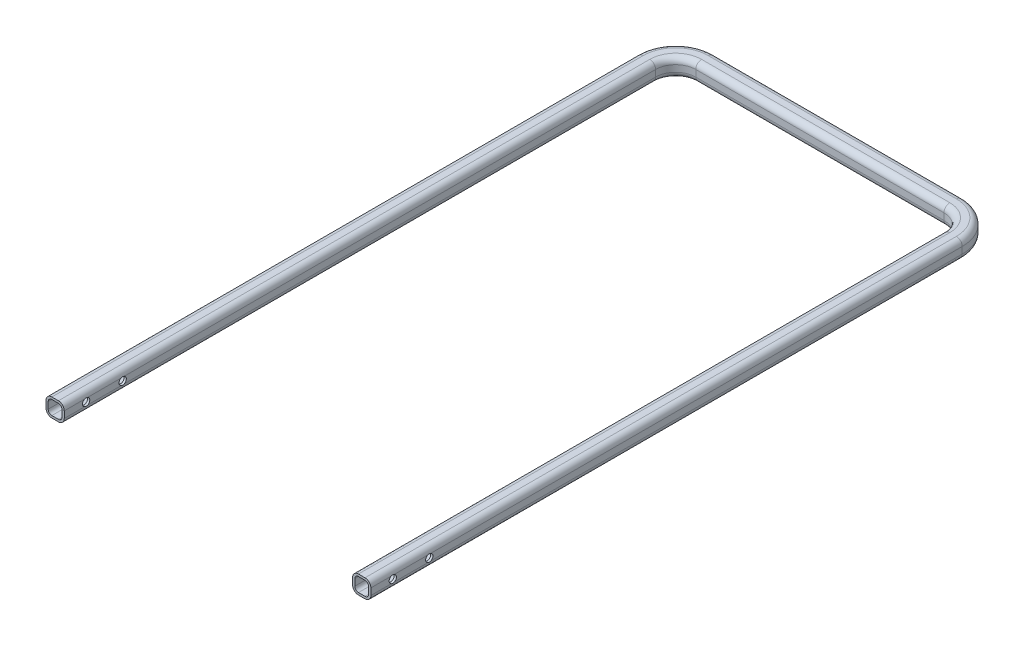
SolidWorks part; units mm, degrees
material "5052-H38, Rod (SS)"
ref_plane "Front Plane" through (0, 0, 0) normal (0, 0, 1) x (1, 0, 0)
ref_plane "Top Plane" through (0, 0, 0) normal (0, 1, 0) x (1, 0, 0)
ref_plane "Right Plane" through (0, 0, 0) normal (1, 0, 0) x (0, 0, -1)
sketch "Sketch1" plane through (0, 0, 0) normal (0, 1, 0) x (1, 0, 0)
  line L0 (0, 0) -> (0, 810)
  line L1 (40, 850) -> (380, 850)
  line L2 (420, 810) -> (420, 0)
  line L3 (0, 560) -> (420, 560) construction
  line L4 (0, 260) -> (420, 260) construction
  line L5 (420, 260) -> (420, 560) construction
  arc A0 (380, 850) -> (420, 810) centre (380, 810) cw
  arc A1 (40, 850) -> (0, 810) centre (40, 810) ccw
  point P7 (420, 850)
  point P10 (0, 850)
  dimension "D3" = 40
  dimension "D4" = 250
  dimension "D1" = 850
  dimension "D2" = 420
  dimension "D5" = 300
ref_plane "Plane1" through (0, 0, 0) normal (0, 0, 1) x (1, 0, 0)
sketch "Sketch3" plane through (0, 0, 0) normal (0, 0, 1) x (1, 0, 0)
  line L1 (-4.5, -9.5) -> (4.5, -9.5)
  line L2 (-9.5, -4.5) -> (-9.5, 4.5)
  line L3 (-4.5, 9.5) -> (4.5, 9.5)
  line L4 (9.5, -4.5) -> (9.5, 4.5)
  line L5 (-9.5, -9.5) -> (9.5, 9.5) construction
  line L6 (-9.5, 9.5) -> (9.5, -9.5) construction
  arc A0 (-4.5, 9.5) -> (-9.5, 4.5) centre (-4.5, 4.5) ccw
  arc A1 (-9.5, -4.5) -> (-4.5, -9.5) centre (-4.5, -4.5) ccw
  arc A2 (4.5, -9.5) -> (9.5, -4.5) centre (4.5, -4.5) ccw
  arc A3 (9.5, 4.5) -> (4.5, 9.5) centre (4.5, 4.5) ccw
  point P0 (0, 0)
  dimension "D3" = 5
  dimension "D1" = 19
  dimension "D2" = 19
sweep "Sweep-Thin1" add profiles "Sketch3" path "Sketch1" parameters "D1"=3
sketch "Sketch4" plane through (0, 0, 0) normal (1, 0, 0) x (0, 0, -1)
  line L0 (0, 0) -> (810, 0) construction
  circle A0 centre (30, 0) radius 5
  circle A1 centre (80, 0) radius 5
  dimension "D1" = 30
  dimension "D2" = 80
extrude "Cut-Extrude2" cut sketch "Sketch4" against normal through all both and the other way through all
ref_plane "Plane4" through (420, 0, 0) normal (-1, 0, 0) x (0, 0, 1)
sketch "Sketch8" plane through (420, 0, 0) normal (-1, 0, 0) x (0, 0, 1)
  line L0 (-560, 0) -> (-260, 0) construction
  line L1 (-410, 0) -> (-410, -61.9086) construction
ref_plane "Plane5" through (0, 0, 0) normal (1, 0, 0) x (0, 0, -1)
